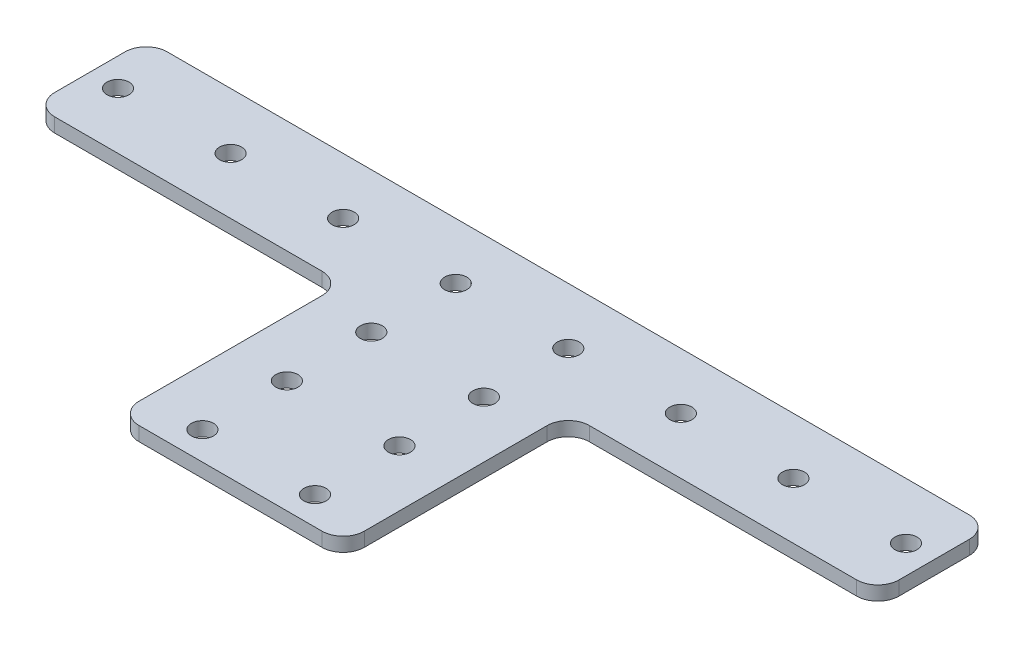
SolidWorks part; units mm, degrees
material "6061-T6 (SS)"
ref_plane "Front Plane" through (0, 0, 0) normal (0, 0, 1) x (1, 0, 0)
ref_plane "Top Plane" through (0, 0, 0) normal (0, 1, 0) x (1, 0, 0)
ref_plane "Right Plane" through (0, 0, 0) normal (1, 0, 0) x (0, 0, -1)
sketch "Sketch1" plane through (0, 0, 0) normal (0, 1, 0) x (1, 0, 0)
  line L0 (95.25, 0) -> (95.25, -50.8) construction
  line L1 (0, 0) -> (190.5, 0)
  line L2 (0, 0) -> (0, 25.4)
  line L3 (0, 25.4) -> (190.5, 25.4)
  line L4 (190.5, 0) -> (190.5, 25.4)
  line L5 (69.85, 0) -> (120.65, 0)
  line L6 (69.85, 0) -> (69.85, -50.8)
  line L7 (69.85, -50.8) -> (120.65, -50.8)
  line L8 (120.65, 0) -> (120.65, -50.8)
  line L13 (0, 12.7) -> (190.5, 12.7) construction
  circle A0 centre (6.35, 12.7) radius 2.4892
  circle A1 centre (31.75, 12.7) radius 2.4892
  circle A2 centre (57.15, 12.7) radius 2.4892
  circle A3 centre (82.55, 12.7) radius 2.4892
  circle A4 centre (107.95, 12.7) radius 2.4892
  circle A5 centre (133.35, 12.7) radius 2.4892
  circle A6 centre (158.75, 12.7) radius 2.4892
  circle A7 centre (184.15, 12.7) radius 2.4892
  circle A23 centre (82.55, -6.35) radius 2.4892
  circle A24 centre (107.95, -6.35) radius 2.4892
  circle A25 centre (107.95, -25.4) radius 2.4892
  circle A26 centre (107.95, -44.45) radius 2.4892
  circle A27 centre (82.55, -25.4) radius 2.4892
  circle A28 centre (82.55, -44.45) radius 2.4892
  point P11 (0, 0)
  point P12 (58.1781, -22.9076)
  point P13 (0, 0)
  dimension "D8" = 4.9784
  dimension "D1" = 50.8
  dimension "D2" = 190.5
  dimension "D3" = 25.4
  dimension "D4" = 2
  dimension "D5" = 3
  dimension "D6" = 19.05
  dimension "D7" = 19.05
  dimension "D10" = 25.4
  dimension "D11" = 6.35
  dimension "D9" = 8
extrude "Boss-Extrude1" add sketch "Sketch1" along normal blind 3.175
fillet "Fillet1" radius 4.7625 8 edges at (120.65, 1.5875, 0) (69.85, 1.5875, 0) (120.65, 1.5875, 50.8) (69.85, 1.5875, 50.8) (0, 1.5875, -25.4) (190.5, 1.5875, -25.4) (190.5, 1.5875, 0) (0, 1.5875, 0)
